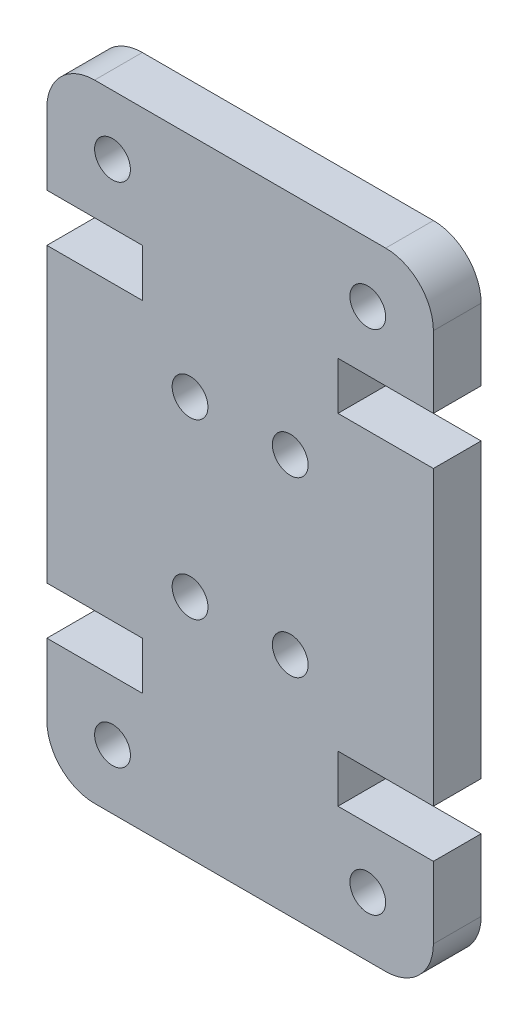
SolidWorks part; units mm, degrees
ref_plane "Front Plane" through (0, 0, 0) normal (0, 0, 1) x (1, 0, 0)
ref_plane "Top Plane" through (0, 0, 0) normal (0, 1, 0) x (1, 0, 0)
ref_plane "Right Plane" through (0, 0, 0) normal (1, 0, 0) x (0, 0, -1)
sketch "Sketch2" plane through (0, 0, 0) normal (0, 0, 1) x (1, 0, 0)
  line L0 (0, 13.13) -> (16.2, 13.13) construction
  line L1 (8.1, 26.26) -> (8.1, 0) construction
  line L2 (0, 7) -> (0, 19.26)
  line L3 (2, 0) -> (14.2, 0)
  line L4 (16.2, 2) -> (16.2, 5)
  line L5 (12.2, 5) -> (16.2, 5)
  line L6 (16.2, 7) -> (12.2, 7)
  line L7 (12.2, 7) -> (12.2, 5)
  line L8 (16.2, 7) -> (16.2, 19.26)
  line L9 (0, 24.26) -> (0, 21.26)
  line L10 (4, 21.26) -> (0, 21.26)
  line L11 (0, 19.26) -> (4, 19.26)
  line L12 (4, 19.26) -> (4, 21.26)
  line L13 (12.2, 19.26) -> (12.2, 21.26)
  line L14 (16.2, 19.26) -> (12.2, 19.26)
  line L15 (12.2, 21.26) -> (16.2, 21.26)
  line L16 (16.2, 24.26) -> (16.2, 21.26)
  line L17 (2, 26.26) -> (14.2, 26.26)
  line L27 (4, 7) -> (4, 5)
  line L30 (0, 7) -> (4, 7)
  line L32 (4, 5) -> (0, 5)
  line L36 (0, 2) -> (0, 5)
  circle A0 centre (13.45, 2.5) radius 0.75
  circle A1 centre (10.2, 9.5) radius 0.75
  arc A2 (16.2, 2) -> (14.2, 0) centre (14.2, 2) cw
  circle A3 centre (2.75, 23.76) radius 0.75
  circle A4 centre (6, 16.76) radius 0.75
  arc A5 (0, 24.26) -> (2, 26.26) centre (2, 24.26) cw
  arc A6 (16.2, 24.26) -> (14.2, 26.26) centre (14.2, 24.26) ccw
  circle A7 centre (10.2, 16.76) radius 0.75
  circle A8 centre (13.45, 23.76) radius 0.75
  arc A17 (0, 2) -> (2, 0) centre (2, 2) ccw
  circle A19 centre (6, 9.5) radius 0.75
  circle A21 centre (2.75, 2.5) radius 0.75
  point P16 (8.1, 13.13)
  dimension "D1" = 1.5
  dimension "D2" = 2
  dimension "D3" = 2.75
  dimension "D4" = 6
  dimension "D5" = 8.1
  dimension "D6" = 2.5
  dimension "D7" = 5
  dimension "D9" = 9.5
  dimension "D10" = 13.13
extrude "Boss-Extrude1" add sketch "Sketch2" along normal blind 2
equation "\"D5@Sketch2\"= \"fingerWidth@parametersSketch@prostheticParameters.SLDPRT\" / 2'Finger Width"
equation "\"D10@Sketch2\"= ( ( \"HL@parametersSketch@prostheticParameters.SLDPRT\" * 0.196 ) - 4 - 6 ) / 2 'PIP Length"
